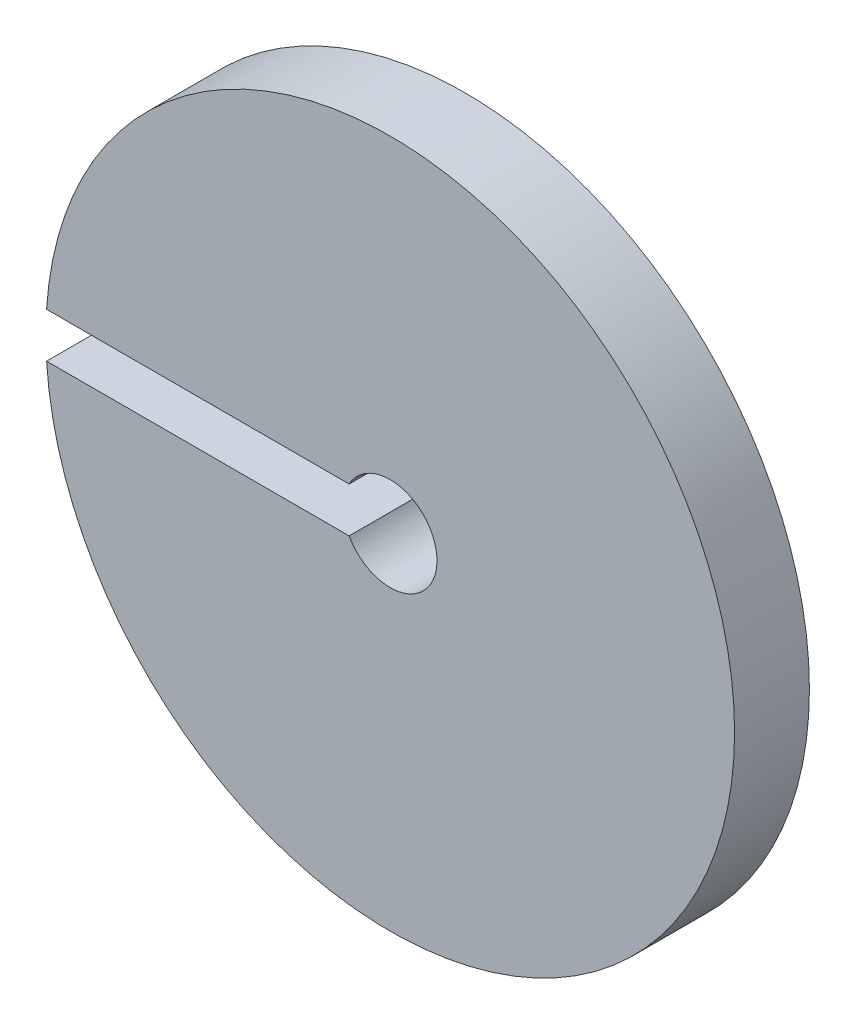
SolidWorks part; units mm, degrees
ref_plane "Front Plane" through (0, 0, 0) normal (0, 0, 1) x (1, 0, 0)
ref_plane "Top Plane" through (0, 0, 0) normal (0, 1, 0) x (1, 0, 0)
ref_plane "Right Plane" through (0, 0, 0) normal (1, 0, 0) x (0, 0, -1)
sketch "Sketch1" plane through (0, 0, 0) normal (0, 0, 1) x (1, 0, 0)
  circle A0 centre (0, 0) radius 23
  dimension "D1" = 46
extrude "Boss-Extrude1" add sketch "Sketch1" along normal blind 5
sketch "Sketch2" plane through (0, 0, 0) normal (0, 0, -1) x (-1, 0, 0)
  circle A0 centre (0, 0) radius 3.125
  dimension "D1" = 6.25
extrude "Cut-Extrude1" cut sketch "Sketch2" against normal through all
sketch "Sketch3" plane through (0, 0, 5) normal (0, 0, 1) x (1, 0, 0)
  circle A0 centre (0, 0) radius 20
  dimension "D1" = 40
sketch "Sketch4" plane through (0, 0, 0) normal (0, 0, -1) x (-1, 0, 0)
  line L1 (2.7415, 1.5) -> (24.773, 1.5)
  line L2 (2.7415, 1.5) -> (2.7415, -1.5)
  line L3 (2.7415, -1.5) -> (24.773, -1.5)
  line L4 (24.773, 1.5) -> (24.773, -1.5)
  circle A0 centre (0, 0) radius 3.125 construction
  dimension "D1" = 3
extrude "Cut-Extrude2" cut sketch "Sketch4" against normal through all
equation "\"mat\"=\"mat@rwv2.assembly\""
equation "\"D1@Boss-Extrude1\"=\"mat\""
